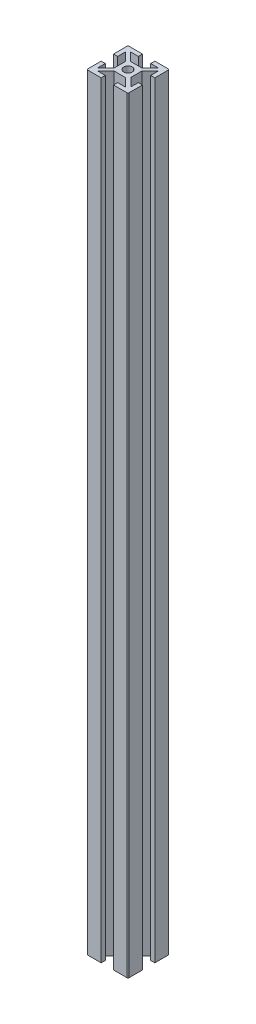
SolidWorks part; units mm, degrees
material "6061 Alloy"
ref_plane "Front Plane" through (0, 0, 0) normal (0, 0, 1) x (1, 0, 0)
ref_plane "Top Plane" through (0, 0, 0) normal (0, 1, 0) x (1, 0, 0)
ref_plane "Right Plane" through (0, 0, 0) normal (1, 0, 0) x (0, 0, -1)
ref_plane "Plane1" through (0, 420, 0) normal (0, 1, 0) x (1, 0, 0)
sketch "Sketch1" plane through (0, 420, 0) normal (0, 1, 0) x (1, 0, 0)
  line L0 (4, 2.7464) -> (8, 6.7464)
  line L1 (8, 6.7464) -> (8, 3)
  line L2 (8, 3) -> (10, 3)
  line L3 (10, 3) -> (10, 9.5)
  line L4 (9.5, 10) -> (3, 10)
  line L5 (3, 10) -> (3, 8)
  line L6 (3, 8) -> (6.8633, 8)
  line L7 (6.8633, 8) -> (2.8633, 4)
  line L8 (2.8633, 4) -> (-2.75, 4)
  line L9 (-2.75, 4) -> (-6.75, 8)
  line L10 (-6.75, 8) -> (-3, 8)
  line L11 (-3, 8) -> (-3, 10)
  line L12 (-3, 10) -> (-9.5, 10)
  line L13 (-10, 9.5) -> (-10, 3)
  line L14 (-10, 3) -> (-8, 3)
  line L15 (-8, 3) -> (-8, 6.75)
  line L16 (-8, 6.75) -> (-4, 2.75)
  line L17 (-4, 2.75) -> (-4, -2.75)
  line L18 (-4, -2.75) -> (-8, -6.75)
  line L19 (-8, -6.75) -> (-8, -3)
  line L20 (-8, -3) -> (-10, -3)
  line L21 (-10, -3) -> (-10, -9.5)
  line L22 (-9.5, -10) -> (-3, -10)
  line L23 (-3, -10) -> (-3, -8)
  line L24 (-3, -8) -> (-6.75, -8)
  line L25 (-6.75, -8) -> (-2.75, -4)
  line L26 (-2.75, -4) -> (2.8685, -4)
  line L27 (2.8685, -4) -> (6.8685, -8)
  line L28 (6.8685, -8) -> (3, -8)
  line L29 (3, -8) -> (3, -10)
  line L30 (3, -10) -> (9.5, -10)
  line L31 (10, -9.5) -> (10, -3)
  line L32 (10, -3) -> (8, -3)
  line L33 (8, -3) -> (8, -6.6652)
  line L34 (8, -6.6652) -> (4, -2.6652)
  line L35 (4, -2.6652) -> (4, 2.7464)
  arc A0 (10, 9.5) -> (9.5, 10) centre (9.5, 9.5) ccw
  arc A1 (-9.5, 10) -> (-10, 9.5) centre (-9.5, 9.5) ccw
  arc A2 (-10, -9.5) -> (-9.5, -10) centre (-9.5, -9.5) ccw
  arc A3 (9.5, -10) -> (10, -9.5) centre (9.5, -9.5) ccw
  circle A4 centre (0, 0) radius 2.1
extrude "Boss-Extrude1" add sketch "Sketch1" against normal blind 371.25
ref_plane "Plane2" through (0, 0, 0) normal (1, 0, 0) x (0, 0, -1)
ref_plane "Plane3" through (0, 0, 0) normal (0, 0, 1) x (1, 0, 0)
